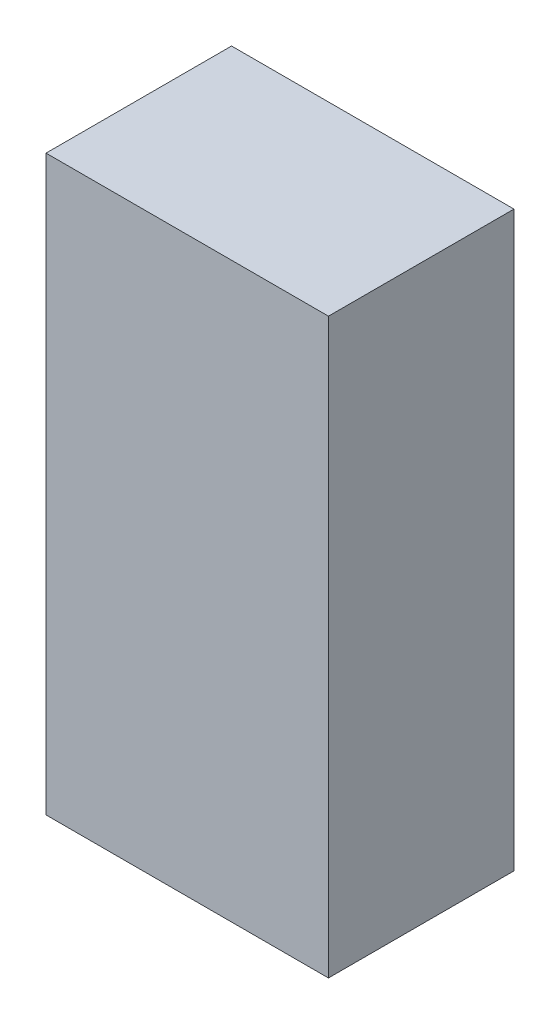
SolidWorks part; units mm, degrees
other "Markup1"
sketch "Sketch2" plane through (13.335, 52.578, 8.89) normal (0.4, 0.515, 0.7581) x (0.8844, 0, -0.4667)
ref_plane "Front Plane" through (0, 0, 0) normal (0, 0, 1) x (1, 0, 0)
ref_plane "Top Plane" through (0, 0, 0) normal (0, 1, 0) x (1, 0, 0)
ref_plane "Right Plane" through (0, 0, 0) normal (1, 0, 0) x (0, 0, -1)
sketch "Sketch1" plane through (0, 0, 0) normal (0, 1, 0) x (1, 0, 0)
  line L1 (-12.954, -8.509) -> (12.954, -8.509)
  line L2 (-12.954, -8.509) -> (-12.954, 8.509)
  line L3 (-12.954, 8.509) -> (12.954, 8.509)
  line L4 (12.954, -8.509) -> (12.954, 8.509)
  line L5 (-12.954, -8.509) -> (12.954, 8.509) construction
  line L6 (-12.954, 8.509) -> (12.954, -8.509) construction
  point P0 (0, 0)
  dimension "D1" = 17.018
  dimension "D2" = 25.908
extrude "Boss-Extrude1" add sketch "Sketch1" along normal blind 52.578
